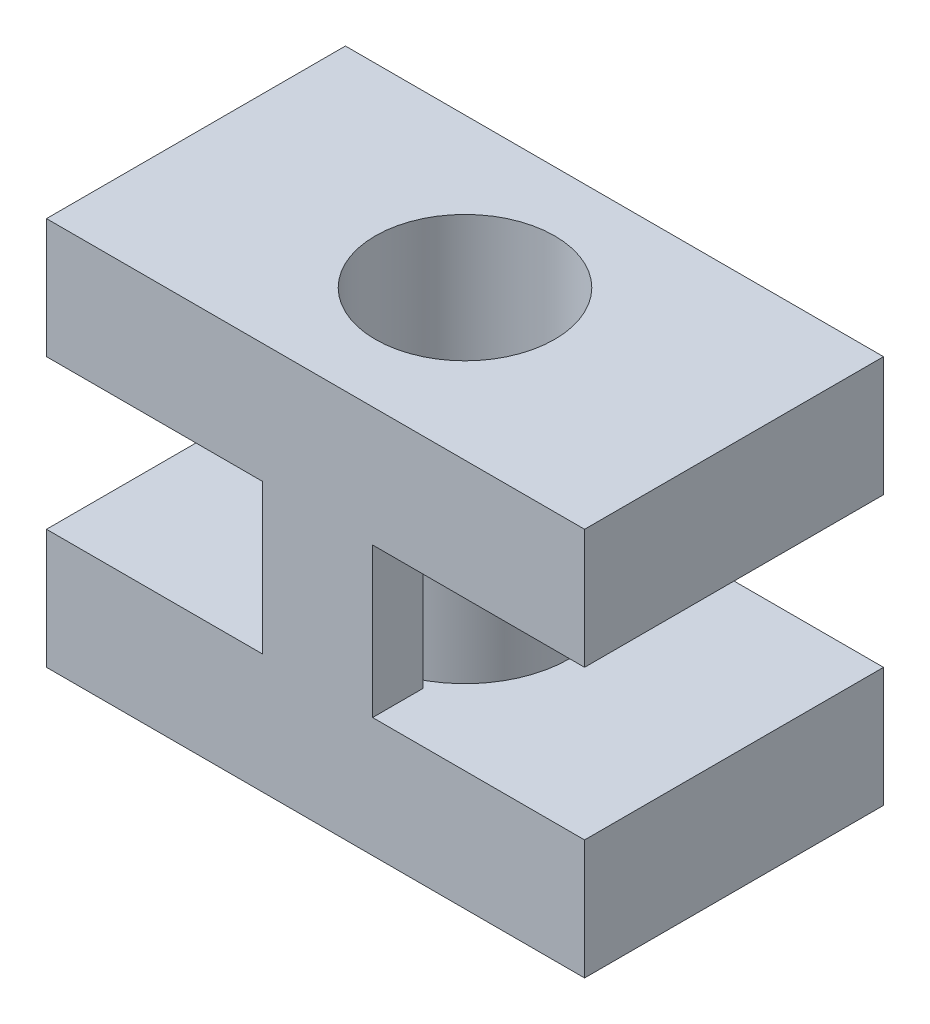
SolidWorks part; units mm, degrees
ref_plane "Front Plane" through (0, 0, 0) normal (0, 0, 1) x (1, 0, 0)
ref_plane "Top Plane" through (0, 0, 0) normal (0, 1, 0) x (1, 0, 0)
ref_plane "Right Plane" through (0, 0, 0) normal (1, 0, 0) x (0, 0, -1)
sketch "Sketch1" plane through (0, 0, 0) normal (0, 1, 0) x (1, 0, 0)
  circle A0 centre (0, 0) radius 1.5
  circle A1 centre (0, 0) radius 1.75
  dimension "D1" = 3
  dimension "D2" = 3.5
extrude "Boss-Extrude1" add sketch "Sketch1" along normal mid plane 6.5
sketch "Sketch2" plane through (0, 3.25, 0) normal (0, 1, 0) x (1, 0, 0)
  line L1 (4.5, -2.5) -> (-4.5, -2.5)
  line L2 (4.5, -2.5) -> (4.5, 2.5)
  line L3 (4.5, 2.5) -> (-4.5, 2.5)
  line L4 (-4.5, -2.5) -> (-4.5, 2.5)
  line L5 (4.5, -2.5) -> (-4.5, 2.5) construction
  line L6 (4.5, 2.5) -> (-4.5, -2.5) construction
  circle A0 centre (0, 0) radius 1.5
  point P0 (0, 0)
  dimension "D1" = 9
  dimension "D2" = 5
extrude "Boss-Extrude2" add sketch "Sketch2" against normal blind 2
mirror "Mirror1" about plane through (0, 0, 0) normal (0, 1, 0) of "Boss-Extrude2"
sketch "Sketch3" plane through (0, -1.25, 0) normal (0, 1, 0) x (1, 0, 0)
  line L0 (0, 1.6577) -> (-0.8902, 1.6577)
  line L1 (-0.8902, 1.6577) -> (-0.8902, 2.5)
  line L2 (4.5, 2.5) -> (-4.5, 2.5) construction
  line L3 (-0.8902, 2.5) -> (0.9544, 2.5)
  line L4 (0.9544, 2.5) -> (0.9544, 1.6577)
  line L5 (0.9544, 1.6577) -> (0, 1.6577)
  line L6 (0, 0) -> (4.5, 0) construction
  line L7 (4.5, -2.5) -> (4.5, 2.5) construction
  line L8 (0.9544, -1.6577) -> (0, -1.6577)
  line L9 (0.9544, -2.5) -> (0.9544, -1.6577)
  line L10 (-0.8902, -2.5) -> (0.9544, -2.5)
  line L11 (-0.8902, -1.6577) -> (-0.8902, -2.5)
  line L12 (0, -1.6577) -> (-0.8902, -1.6577)
extrude "Boss-Extrude3" add sketch "Sketch3" along normal up to surface (2.5 mm away) up to face at (0, 1.25, 0)
